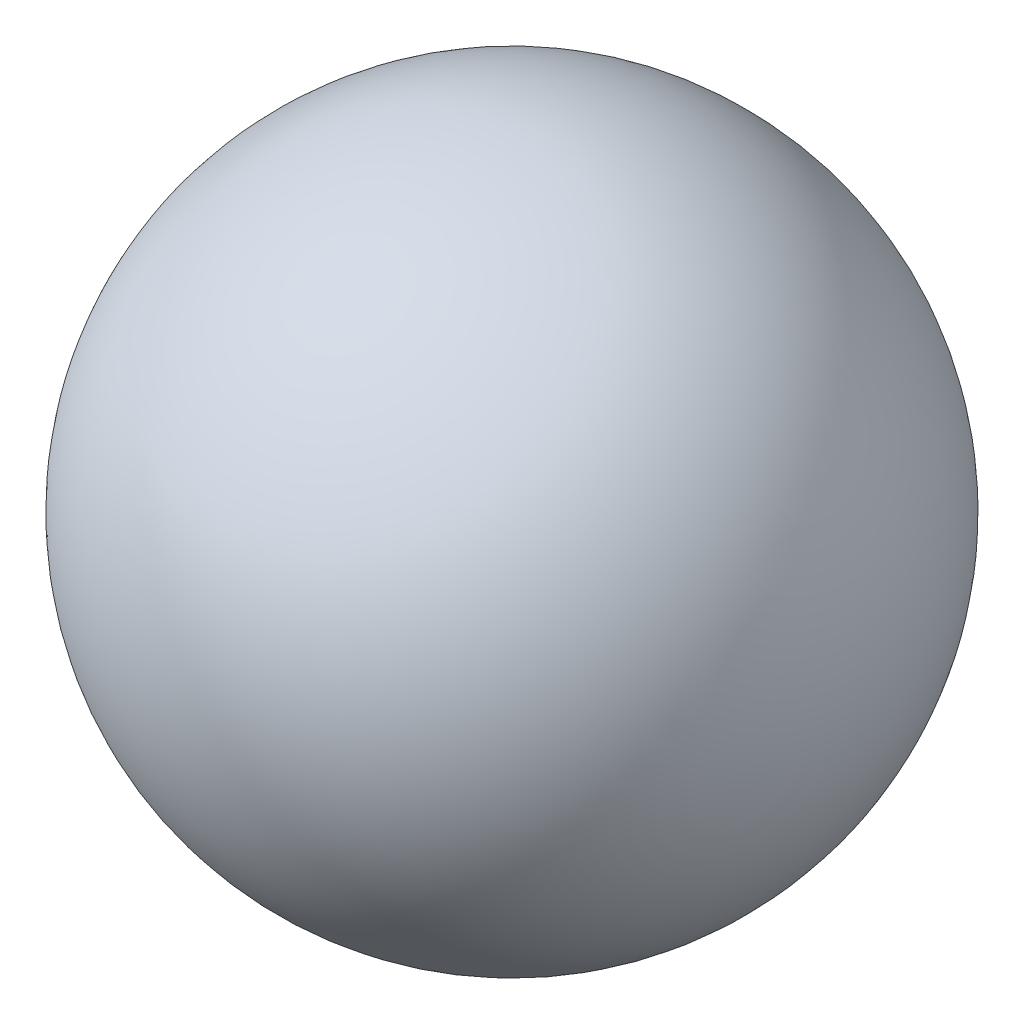
SolidWorks part; units mm, degrees
ref_plane "Front Plane" through (0, 0, 0) normal (0, 0, 1) x (1, 0, 0)
ref_plane "Top Plane" through (0, 0, 0) normal (0, 1, 0) x (1, 0, 0)
ref_plane "Right Plane" through (0, 0, 0) normal (1, 0, 0) x (0, 0, -1)
sketch "Sketch1" plane through (0, 0, 0) normal (0, 0, 1) x (1, 0, 0)
  line L0 (-12, 0) -> (12, 0)
  arc A0 (12, 0) -> (-12, 0) centre (0, 0) cw
  point P5 (0, 0)
  point P6 (0, 0)
  point P7 (-12.3193, 0)
  dimension "D1" = 24
revolve "Revolve1" add sketch "Sketch1" angle 360 about L0
